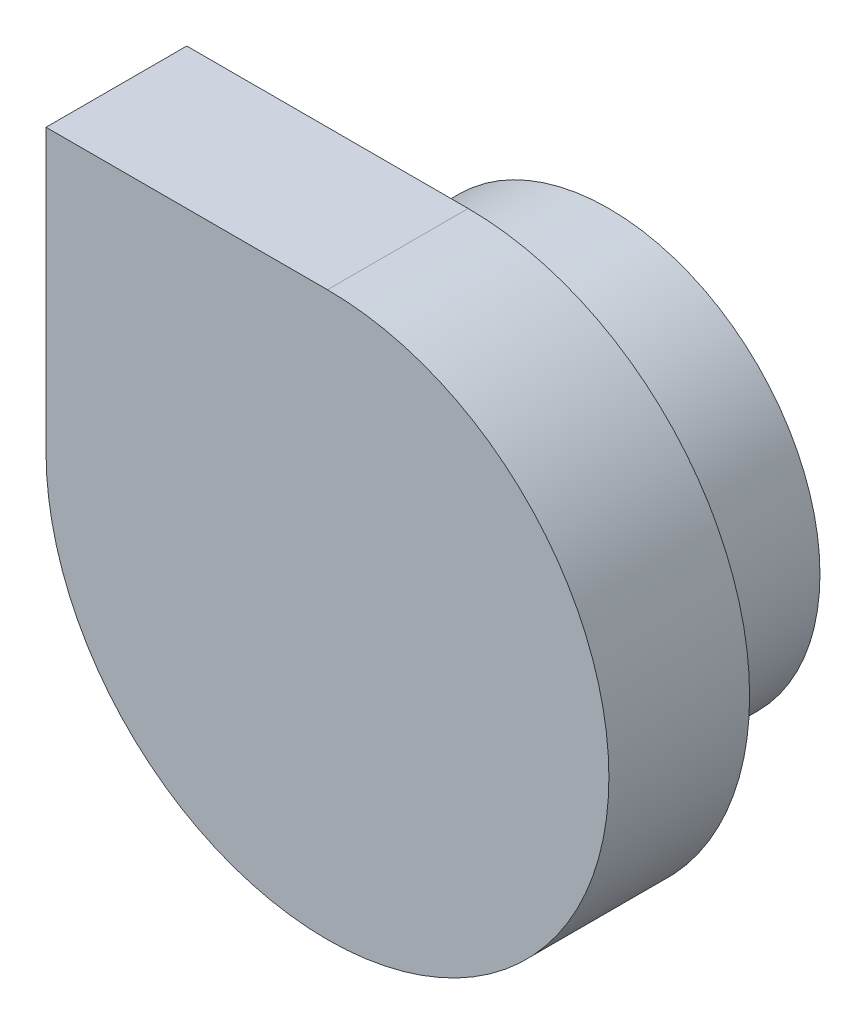
SolidWorks part; units mm, degrees
ref_plane "Plan de face" through (0, 0, 0) normal (0, 0, 1) x (1, 0, 0)
ref_plane "Plan de dessus" through (0, 0, 0) normal (0, 1, 0) x (1, 0, 0)
ref_plane "Plan de droite" through (0, 0, 0) normal (1, 0, 0) x (0, 0, -1)
sketch "Esquisse1" plane through (0, 0, 0) normal (0, 0, 1) x (1, 0, 0)
  line L0 (-100, 0) -> (-100, 100)
  line L1 (-100, 100) -> (0, 100)
  arc A0 (-100, 0) -> (0, 100) centre (0, 0) ccw
  dimension "D1" = 100
extrude "Boss.-Extru.1" add sketch "Esquisse1" against normal blind 50
sketch "Esquisse2" plane through (0, 0, -50) normal (0, 0, -1) x (-1, 0, 0)
  circle A0 centre (0, 0) radius 75
  circle A1 centre (0, 0) radius 50
  dimension "D1" = 150
  dimension "D2" = 100
extrude "Boss.-Extru.2" add sketch "Esquisse2" along normal blind 50
